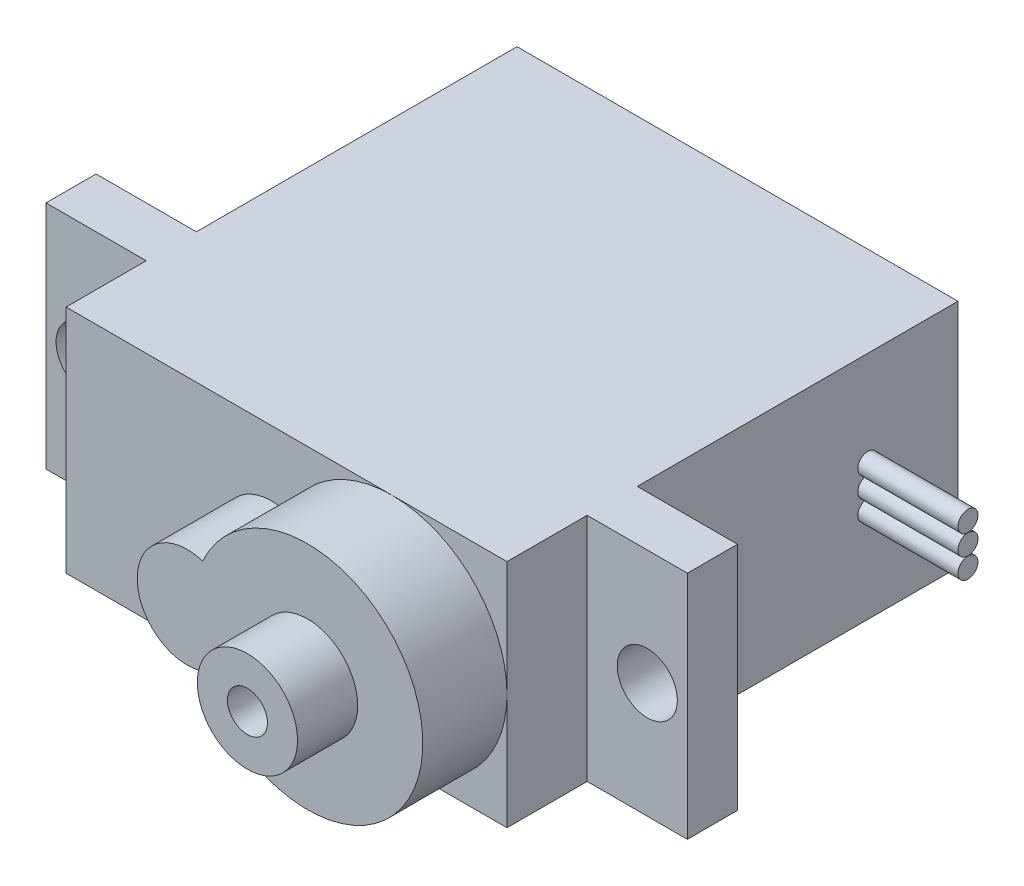
SolidWorks part; units mm, degrees
ref_plane "正面" through (0, 0, 0) normal (0, 0, 1) x (1, 0, 0)
ref_plane "平面" through (0, 0, 0) normal (0, 1, 0) x (1, 0, 0)
ref_plane "右側面" through (0, 0, 0) normal (1, 0, 0) x (0, 0, -1)
sketch "ｽｹｯﾁ1" plane through (0, 0, 0) normal (0, 0, 1) x (1, 0, 0)
  line L1 (0, 0) -> (22, 0)
  line L2 (0, 0) -> (0, 11.5)
  line L3 (0, 11.5) -> (22, 11.5)
  line L4 (22, 0) -> (22, 11.5)
  line L5 (0, 0) -> (22, 11.5) construction
  line L6 (0, 11.5) -> (22, 0) construction
  point P4 (11, 5.75)
  dimension "D1" = 11.5
  dimension "D2" = 22
extrude "ﾎﾞｽ - 押し出し1" add sketch "ｽｹｯﾁ1" along normal blind 16
sketch "ｽｹｯﾁ2" plane through (0, 0, 16) normal (0, 0, 1) x (1, 0, 0)
  line L0 (0, 11.5) -> (22, 11.5) construction
  line L1 (27, 0) -> (-5, 0)
  line L2 (27, 0) -> (27, 11.5)
  line L3 (27, 11.5) -> (-5, 11.5)
  line L4 (-5, 0) -> (-5, 11.5)
  line L5 (27, 0) -> (-5, 11.5) construction
  line L6 (27, 11.5) -> (-5, 0) construction
  point P0 (11, 5.75)
  dimension "D1" = 32
extrude "ﾎﾞｽ - 押し出し2" add sketch "ｽｹｯﾁ2" along normal blind 2.5
sketch "ｽｹｯﾁ3" plane through (0, 0, 18.5) normal (0, 0, 1) x (1, 0, 0)
  line L4 (0, 0) -> (22, 0)
  line L5 (22, 0) -> (22, 11.5)
  line L6 (22, 11.5) -> (0, 11.5)
  line L7 (0, 11.5) -> (0, 0)
  line L8 (0, 0) -> (22, 0)
  line L9 (22, 0) -> (22, 11.5)
  line L10 (22, 11.5) -> (0, 11.5)
  line L11 (0, 11.5) -> (0, 0)
  dimension "D1" = 0
extrude "ﾎﾞｽ - 押し出し3" add sketch "ｽｹｯﾁ3" along normal blind 4
sketch "ｽｹｯﾁ4" plane through (0, 0, 22.5) normal (0, 0, 1) x (1, 0, 0)
  line L1 (10.25, 5.75) -> (16.25, 5.75) construction
  line L2 (0, 11.5) -> (22, 11.5) construction
  line L3 (22, 0) -> (22, 11.5) construction
  line L4 (0, 0) -> (22, 0) construction
  arc A0 (11.0156, 8.1299) -> (11.0156, 3.3701) centre (10.25, 5.75) ccw
  arc A1 (11.0156, 3.3701) -> (11.0156, 8.1299) centre (16.25, 5.75) ccw
  point P8 (0, 0)
  point P9 (11.8887, 4.0028)
  dimension "D1" = 5
  dimension "D2" = 6
extrude "ﾎﾞｽ - 押し出し4" add sketch "ｽｹｯﾁ4" along normal blind 4.2
sketch "ｽｹｯﾁ5" plane through (0, 0, 18.5) normal (0, 0, 1) x (1, 0, 0)
  line L0 (-5, 5.75) -> (27, 5.75) construction
  line L1 (-5, 11.5) -> (-5, 0) construction
  line L2 (27, 0) -> (27, 11.5) construction
  circle A0 centre (-3, 5.75) radius 1.5
  circle A1 centre (25, 5.75) radius 1.5
  dimension "D2" = 3
  dimension "D1" = 28
  dimension "D3" = 14
extrude "ｶｯﾄ - 押し出し1" cut sketch "ｽｹｯﾁ5" against normal through all
sketch "ｽｹｯﾁ6" plane through (22, 0, 0) normal (1, 0, 0) x (0, 0, -1)
  line L0 (-5, 11.5) -> (-5, 0) construction
  line L1 (-16, 11.5) -> (0, 11.5) construction
  line L2 (-16, 0) -> (0, 0) construction
  line L3 (-4.5, 11.5) -> (-4.5, 0) construction
  line L4 (0, 0) -> (0, 11.5) construction
  circle A0 centre (-4.5, 5.75) radius 0.5
  circle A1 centre (-4.5, 6.76) radius 0.5
  circle A3 centre (-4.5, 4.74) radius 0.5
  dimension "D2" = 1
  dimension "D1" = 5
  dimension "D3" = 1.01
  dimension "D4" = 1.01
extrude "ﾎﾞｽ - 押し出し6" add sketch "ｽｹｯﾁ6" along normal blind 5 separate body
sketch "ｽｹｯﾁ7" plane through (0, 0, 26.7) normal (0, 0, 1) x (1, 0, 0)
  circle A0 centre (16.25, 5.75) radius 2.5
  circle A1 centre (16.25, 5.75) radius 1
  dimension "D1" = 2
  dimension "D2" = 5
extrude "ﾎﾞｽ - 押し出し7" add sketch "ｽｹｯﾁ7" along normal blind 3 separate body
sketch "ｽｹｯﾁ8" plane through (0, 0, 0) normal (0, -1, 0) x (1, 0, 0)
  text T0 "SG-90"
  point P1 (0, 0)
extrude "ｶｯﾄ - 押し出し2" cut sketch "ｽｹｯﾁ8" against normal blind 2
equation "\"D3@ｽｹｯﾁ5\"=\"D1@ｽｹｯﾁ5\"/2"
equation "\"D4@ｽｹｯﾁ6\"=\"D3@ｽｹｯﾁ6\""
